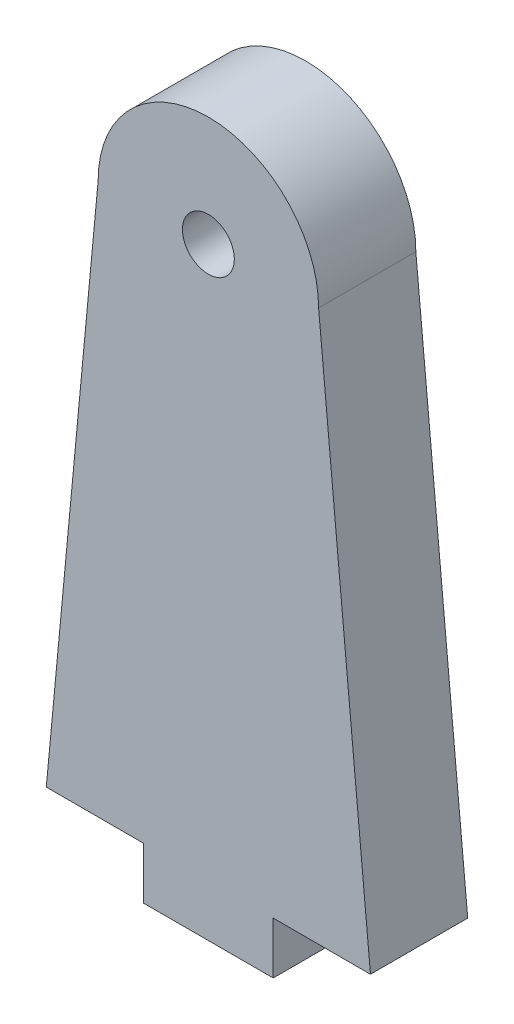
SolidWorks part; units mm, degrees
ref_plane "Front Plane" through (0, 0, 0) normal (0, 0, 1) x (1, 0, 0)
ref_plane "Top Plane" through (0, 0, 0) normal (0, 1, 0) x (1, 0, 0)
ref_plane "Right Plane" through (0, 0, 0) normal (1, 0, 0) x (0, 0, -1)
sketch "Sketch1" plane through (0, 0, 0) normal (0, 0, 1) x (1, 0, 0)
  line L0 (0, 0) -> (0, 108.3965) construction
  line L1 (-10, 0) -> (10, 0)
  line L2 (10, 0) -> (10, 8)
  line L3 (10, 8) -> (25, 8)
  line L4 (17, 93) -> (25, 8)
  line L5 (-10, 0) -> (-10, 8)
  line L6 (-10, 8) -> (-25, 8)
  line L7 (-17, 93) -> (-25, 8)
  circle A0 centre (0, 93) radius 7
  arc A1 (17, 93) -> (-17, 93) centre (0, 93) ccw
  dimension "D1" = 85
  dimension "D3" = 17
  dimension "D4" = 14
  dimension "D2" = 8
  dimension "D5" = 15
  dimension "D6" = 20
extrude "Boss-Extrude1" add sketch "Sketch1" along normal blind 15
hole_wizard "Ø8.0mm Dowel Hole1" positions "3DSketch1" profile "Sketch2" hole size "Ø8.0" standard "ANSI Metric"
sketch3d "3DSketch1"
  point P0 (0, 0, 7.5)
  point P3 (0, 0, 0)
  dimension "D1" = 0
  dimension "D2" = 7.5
sketch "Sketch2" plane through (0, 0, 7.5) normal (1, 0, 0) x (0, 0, -1)
  line L0 (0, 0) -> (0, 32.4034)
  line L1 (0, 32.4034) -> (4, 30)
  line L2 (4, 30) -> (4, 0)
  line L5 (4, 0) -> (0, 0)
  line L10 (0, 32.4034) -> (-4, 30) construction
  line L11 (0, -6.35) -> (0, 107.95) construction
  dimension "Hole Dia." = 8
  dimension "Hole Depth" = 30
  dimension "Drill Angle" = 118
sketch "Sketch3" plane through (0, 0, 15) normal (0, 0, 1) x (1, 0, 0)
  circle A0 centre (0, 93) radius 4
  circle M9 centre (0, 93) radius 7
  dimension "D1" = 8
extrude "Boss-Extrude2" add sketch "Sketch3" against normal through all contours A0 M9
